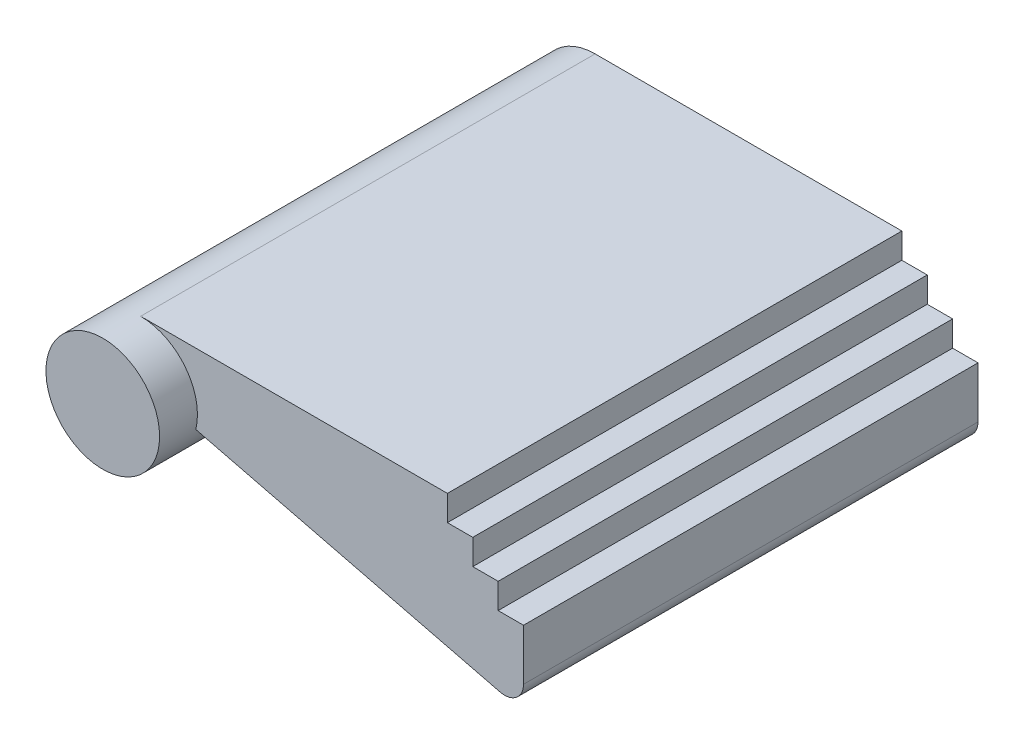
SolidWorks part; units mm, degrees
ref_plane "前视基准面" through (0, 0, 0) normal (0, 0, 1) x (1, 0, 0)
ref_plane "上视基准面" through (0, 0, 0) normal (0, 1, 0) x (1, 0, 0)
ref_plane "右视基准面" through (0, 0, 0) normal (1, 0, 0) x (0, 0, -1)
sketch "草图1" plane through (0, 0, 0) normal (0, 0, 1) x (1, 0, 0)
  circle A0 centre (0, 0) radius 1.5
  dimension "D1" = 3
extrude "凸台-拉伸1" add sketch "草图1" along normal blind 13
sketch "草图2" plane through (0, 0, 0) normal (0, 0, 1) x (1, 0, 0)
  line L0 (0, 1.5) -> (8.1, 1.5)
  line L1 (8.1, 1.5) -> (8.1, 0.83)
  line L2 (8.1, 0.83) -> (8.77, 0.83)
  line L3 (8.77, 0.83) -> (8.77, 0.16)
  line L4 (8.77, 0.16) -> (9.44, 0.16)
  line L5 (9.44, 0.16) -> (9.44, -0.51)
  line L6 (10.11, -2.5) -> (0, 0)
  line L7 (0, 0) -> (0, 1.5)
  line L8 (9.44, -0.51) -> (10.11, -0.51)
  line L9 (10.11, -0.51) -> (10.11, -2.5)
  circle A0 centre (0, 0) radius 1.5 construction
  dimension "D1" = 8.1
  dimension "D2" = 0.67
  dimension "D3" = 0.67
  dimension "D4" = 0.67
  dimension "D5" = 0.67
  dimension "D6" = 0.67
  dimension "D7" = 4
  dimension "D8" = 0.67
extrude "凸台-拉伸2" add sketch "草图2" along normal blind 12
fillet "圆角1" radius 0.5 1 edges at (10.11, -2.5, 6)
